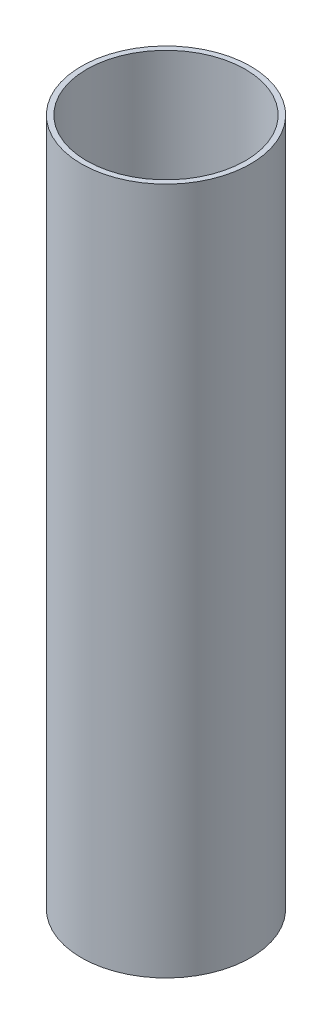
SolidWorks part; units mm, degrees
ref_plane "前视基准面" through (0, 0, 0) normal (0, 0, 1) x (1, 0, 0)
ref_plane "上视基准面" through (0, 0, 0) normal (0, 1, 0) x (1, 0, 0)
ref_plane "右视基准面" through (0, 0, 0) normal (1, 0, 0) x (0, 0, -1)
sketch "草图1" plane through (0, 0, 0) normal (0, 1, 0) x (1, 0, 0)
  circle A0 centre (0, 0) radius 16
  circle A1 centre (0, 0) radius 15
extrude "凸台-拉伸1" add sketch "草图1" along normal blind 130 contours A0 | A1
